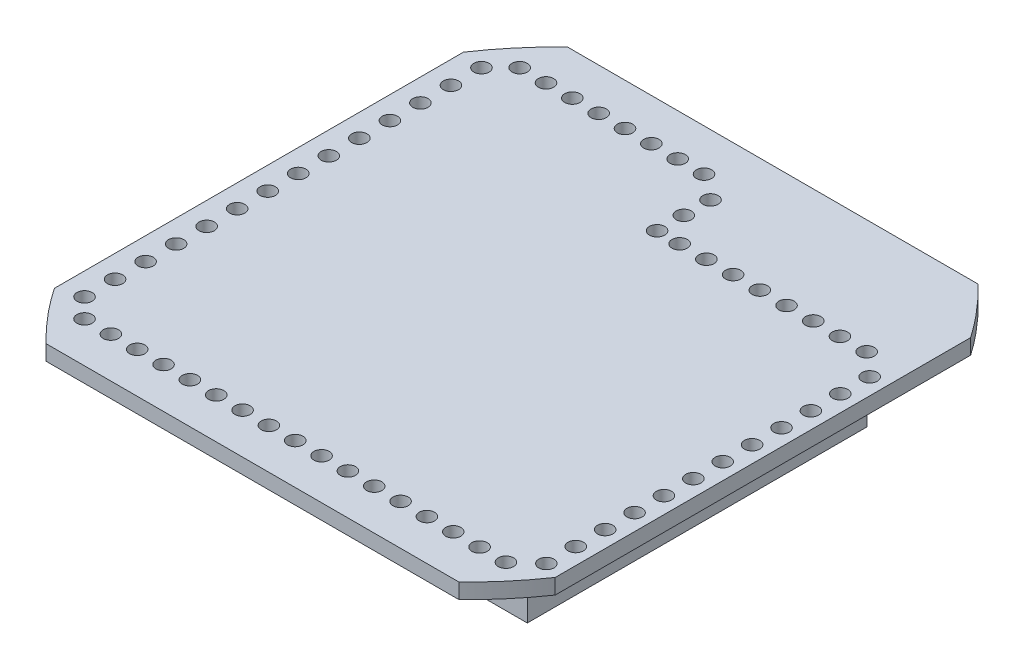
SolidWorks part; units mm, degrees
ref_plane "Front Plane" through (0, 0, 0) normal (0, 0, 1) x (1, 0, 0)
ref_plane "Top Plane" through (0, 0, 0) normal (0, 1, 0) x (1, 0, 0)
ref_plane "Right Plane" through (0, 0, 0) normal (1, 0, 0) x (0, 0, -1)
sketch "Sketch1" plane through (0, 0, 0) normal (0, 1, 0) x (1, 0, 0)
  line L1 (0, 0) -> (115, 0)
  line L2 (0, 0) -> (0, 89)
  line L3 (0, 89) -> (115, 89)
  line L4 (115, 0) -> (115, 89)
  line L5 (2, 2) -> (113, 2)
  line L6 (2, 2) -> (2, 87)
  line L7 (2, 87) -> (113, 87)
  line L8 (113, 2) -> (113, 87)
  line L9 (115, 89) -> (62, 89)
  line L13 (112, 89) -> (64, 89)
  line L17 (112, 89) -> (115, 89)
extrude "Boss-Extrude2" add sketch "Sketch1" along normal blind 10 contours L1 L4 L3 L9 L2 L8 L5 L6 L7
sketch "Sketch5" plane through (0, 10, 0) normal (0, 1, 0) x (1, 0, 0)
  line L0 (54, 108) -> (54, 89)
  line L3 (54, 108) -> (0, 108)
  line L4 (0, 89) -> (0, 108)
  line L5 (52, 89) -> (2, 89)
  line L6 (52, 89) -> (52, 106)
  line L7 (52, 106) -> (2, 106)
  line L8 (2, 89) -> (2, 106)
  line L9 (54, 89) -> (52, 89)
  line L10 (0, 89) -> (2, 89)
extrude "Boss-Extrude3" add sketch "Sketch5" against normal blind 10
sketch "Sketch6" plane through (0, 10, 0) normal (0, 1, 0) x (1, 0, 0)
  line L1 (-25, 133) -> (139, 133)
  line L2 (-25, 133) -> (-25, -25)
  line L3 (-25, -25) -> (139, -25)
  line L4 (139, 133) -> (139, -25)
extrude "Boss-Extrude4" add sketch "Sketch6" along normal blind 4
sketch "Sketch9" plane through (0, 10, 0) normal (0, -1, 0) x (1, 0, 0)
  circle A0 centre (2, 3) radius 2
  circle A1 centre (8.9, 3) radius 2
  circle A2 centre (15.8, 3) radius 2
  circle A3 centre (22.7, 3) radius 2
  circle A4 centre (29.6, 3) radius 2
  circle A5 centre (36.5, 3) radius 2
  circle A6 centre (43.4, 3) radius 2
  circle A7 centre (50.3, 3) radius 2
  circle A8 centre (57.2, 3) radius 2
  circle A9 centre (64.1, 3) radius 2
  circle A10 centre (71, 3) radius 2
  circle A11 centre (77.9, 3) radius 2
  circle A12 centre (-3, -2) radius 2
  circle A13 centre (-3, -10) radius 2
  circle A14 centre (-3, -18) radius 2
  circle A15 centre (-3, -26) radius 2
  circle A16 centre (-3, -34) radius 2
  circle A17 centre (-3, -42) radius 2
  circle A18 centre (-3, -50) radius 2
  circle A19 centre (-3, -58) radius 2
  circle A20 centre (-3, -66) radius 2
  circle A21 centre (-3, -74) radius 2
  circle A22 centre (-3, -82) radius 2
  circle A23 centre (-3, -90) radius 2
  circle A24 centre (-3, -98) radius 2
  circle A25 centre (-3, -106) radius 2
  circle A26 centre (118, -2) radius 2
  circle A27 centre (118, -9.7) radius 2
  circle A28 centre (118, -17.4) radius 2
  circle A29 centre (118, -25.1) radius 2
  circle A30 centre (118, -32.8) radius 2
  circle A31 centre (118, -40.5) radius 2
  circle A32 centre (118, -48.2) radius 2
  circle A33 centre (118, -55.9) radius 2
  circle A34 centre (118, -63.6) radius 2
  circle A35 centre (118, -71.3) radius 2
  circle A36 centre (118, -79) radius 2
  circle A37 centre (118, -86.7) radius 2
  circle A38 centre (2, -111) radius 2
  circle A39 centre (8.9, -111) radius 2
  circle A40 centre (15.8, -111) radius 2
  circle A41 centre (22.7, -111) radius 2
  circle A42 centre (29.6, -111) radius 2
  circle A43 centre (36.5, -111) radius 2
  circle A44 centre (43.4, -111) radius 2
  circle A45 centre (50.3, -111) radius 2
  circle A46 centre (57, -106) radius 2
  circle A47 centre (57, -99) radius 2
  circle A48 centre (57, -92) radius 2
  circle A49 centre (111.9167, -92) radius 2
  circle A50 centre (104.9167, -92) radius 2
  circle A51 centre (97.9167, -92) radius 2
  circle A52 centre (90.9167, -92) radius 2
  circle A53 centre (83.9167, -92) radius 2
  circle A54 centre (76.9167, -92) radius 2
  circle A55 centre (69.9167, -92) radius 2
  circle A56 centre (62.9167, -92) radius 2
  circle A57 centre (84.8, 3) radius 2
  circle A58 centre (91.7, 3) radius 2
  circle A59 centre (98.6, 3) radius 2
  circle A60 centre (105.5, 3) radius 2
  circle A61 centre (112.4, 3) radius 2
  dimension "D1" = 17
  dimension "D2" = 14
  dimension "D3" = 12
  dimension "D4" = 8
  dimension "D5" = 3
  dimension "D6" = 8
extrude "Cut-Extrude2" cut sketch "Sketch9" against normal blind 4
sketch "Sketch10" plane through (0, 10, 0) normal (0, -1, 0) x (-1, 0, 0)
  line L2 (-153.6077, 149.6319) -> (33.2648, 149.6319)
  line L3 (-153.6077, 149.6319) -> (-153.6077, -45.7792)
  line L4 (-153.6077, -45.7792) -> (33.2648, -45.7792)
  line L5 (33.2648, 149.6319) -> (33.2648, -45.7792)
  ellipse E0 centre (-57, 54) end of major axis (-54.165, -35.9553) minor radius 82
extrude "Cut-Extrude3" cut sketch "Sketch10" against normal blind 4
sketch "Sketch12" plane through (0, 10, 0) normal (0, -1, 0) x (1, 0, 0)
  line L1 (-11.688, 27.2174) -> (124.204, 27.2174)
  line L2 (-11.688, 27.2174) -> (-11.688, 13.6494)
  line L3 (-11.688, 13.6494) -> (124.204, 13.6494)
  line L4 (124.204, 27.2174) -> (124.204, 13.6494)
extrude "Cut-Extrude4" cut sketch "Sketch12" against normal blind 4
sketch "Sketch13" plane through (0, 10, 0) normal (0, -1, 0) x (-1, 0, 0)
  line L1 (3.2664, 121.9588) -> (-126.2423, 121.9588)
  line L2 (3.2664, 121.9588) -> (3.2664, 142.6888)
  line L3 (3.2664, 142.6888) -> (-126.2423, 142.6888)
  line L4 (-126.2423, 121.9588) -> (-126.2423, 142.6888)
extrude "Cut-Extrude5" cut sketch "Sketch13" against normal blind 4
sketch "Sketch14" plane through (0, 0, 0) normal (0, -1, 0) x (1, 0, 0)
sketch "Sketch15" plane through (0, 10, 0) normal (0, -1, 0) x (-1, 0, 0)
  line L1 (8.8913, 0) -> (30.6389, 0)
  line L2 (8.8913, 0) -> (8.8913, 111.1512)
  line L3 (8.8913, 111.1512) -> (30.6389, 111.1512)
  line L4 (30.6389, 0) -> (30.6389, 111.1512)
  line L5 (-122.3135, 0) -> (-174.4756, 0)
  line L6 (-122.3135, 0) -> (-122.3135, 113.8739)
  line L7 (-122.3135, 113.8739) -> (-174.4756, 113.8739)
  line L8 (-174.4756, 0) -> (-174.4756, 113.8739)
  ellipse E0 centre (-57, 54) end of major axis (-54.165, -35.9553) minor radius 82 (-2.5563, -13.6494) -> (25, 52.1895) ccw construction
  ellipse E1 centre (-57, 54) end of major axis (-54.165, -35.9553) minor radius 82 (-139, 53.246) -> (-110.72, -13.6494) ccw construction
extrude "Cut-Extrude6" cut sketch "Sketch15" against normal blind 4
equation "\"12i\"=4"
